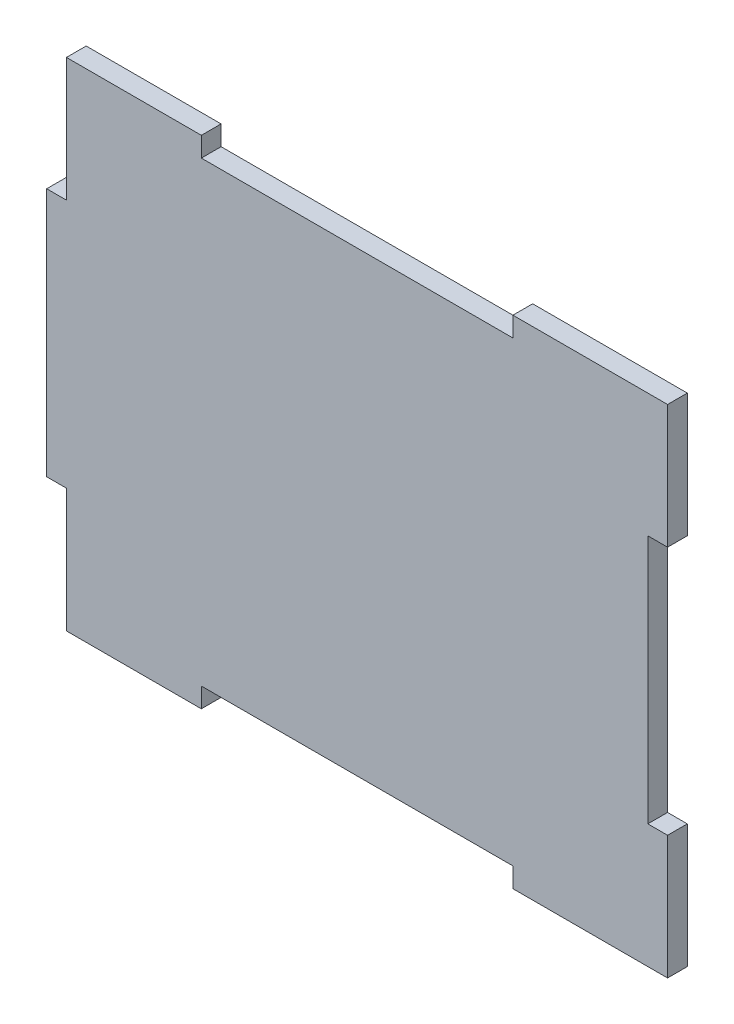
SolidWorks part; units mm, degrees
ref_plane "Front Plane" through (0, 0, 0) normal (0, 0, 1) x (1, 0, 0)
ref_plane "Top Plane" through (0, 0, 0) normal (0, 1, 0) x (1, 0, 0)
ref_plane "Right Plane" through (0, 0, 0) normal (1, 0, 0) x (0, 0, -1)
sketch "Sketch3" plane through (0, 0, 0) normal (0, 0, 1) x (1, 0, 0)
  line L1 (50, -40) -> (-50, -40)
  line L2 (50, -40) -> (50, 40)
  line L3 (50, 40) -> (-50, 40)
  line L4 (-50, -40) -> (-50, 40)
  line L5 (50, -40) -> (-50, 40) construction
  line L6 (50, 40) -> (-50, -40) construction
  point P0 (0, 0)
  dimension "D1" = 100
  dimension "D2" = 80
extrude "Boss-Extrude1" add sketch "Sketch3" along normal blind 3.18
sketch "Sketch4" plane through (0, 0, 3.18) normal (0, 0, 1) x (1, 0, 0)
  line L0 (50, 40) -> (-50, 40) construction
  line L1 (-25.09, 40) -> (25.09, 40)
  line L2 (-25.09, 40) -> (-25.09, 36.82)
  line L3 (-25.09, 36.82) -> (25.09, 36.82)
  line L4 (25.09, 40) -> (25.09, 36.82)
  line L7 (0, 0) -> (0, 96.8251) construction
  point P8 (0, 40)
  dimension "D1" = 3.18
  dimension "D2" = 50.18
extrude "Cut-Extrude1" cut sketch "Sketch4" against normal up to surface (3.18 mm away) up to face at (0, 0, 0)
mirror "Mirror1" about plane through (0, 0, 0) normal (0, 1, 0) of "Cut-Extrude1"
sketch "Sketch5" plane through (0, 0, 3.18) normal (0, 0, 1) x (1, 0, 0)
  line L0 (50, -40) -> (50, 40) construction
  line L1 (50, 20.09) -> (46.82, 20.09)
  line L2 (50, 20.09) -> (50, -20.09)
  line L3 (50, -20.09) -> (46.82, -20.09)
  line L4 (46.82, 20.09) -> (46.82, -20.09)
  line L7 (0, 0) -> (79.7513, 0) construction
  point P8 (50, 0)
  dimension "D1" = 3.18
  dimension "D2" = 40.18
extrude "Cut-Extrude2" cut sketch "Sketch5" against normal up to surface (3.18 mm away) up to face at (0, 0, 0)
sketch "Sketch6" plane through (0, 0, 3.18) normal (0, 0, 1) x (1, 0, 0)
  line L0 (-25.09, 40) -> (-50, 40) construction
  line L1 (-46.82, 40) -> (-50, 40)
  line L2 (-46.82, 40) -> (-46.82, 20.09)
  line L3 (-46.82, 20.09) -> (-50, 20.09)
  line L4 (-50, 40) -> (-50, 20.09)
  line L5 (-50, 40) -> (-50, -40) construction
  line L6 (-50, -40) -> (-25.09, -40) construction
  dimension "D1" = 3.18
  dimension "D3" = 60.09
  dimension "D2" = 19.91
extrude "Cut-Extrude3" cut sketch "Sketch6" against normal up to surface (3.18 mm away) up to face at (12.1025, 0, 0)
mirror "Mirror2" about plane through (0, 0, 0) normal (0, 1, 0) of "Cut-Extrude3"
sketch "Sketch7" [suppressed] plane through (0, 0, 0) normal (0, 0, -1) x (-1, 0, 0)
  line L1 (46.82, -40) -> (46.82, -20.09) construction
  line L2 (-3.18, -25) -> (16.82, -25) construction
  line L4 (-25.09, -40) -> (-50, -40) construction
  circle A0 centre (16.82, -25) radius 3.18
  circle A1 centre (-3.18, -25) radius 3.935
  dimension "D1" = 20
  dimension "D2" = 30
  dimension "D3" = 6.36
  dimension "D4" = 7.87
  dimension "D5" = 15
extrude "Cut-Extrude4" [suppressed] cut sketch "Sketch7" against normal up to surface (3.18 mm away)
sketch "Sketch8" [suppressed] plane through (0, 0, 0) normal (0, 0, -1) x (-1, 0, 0)
  line L1 (-46.82, -20.09) -> (-46.82, 20.09) construction
  line L2 (-25.09, 36.82) -> (25.09, 36.82) construction
  line L3 (-33.52, 23.44) -> (-22.52, 23.44)
  line L4 (-33.52, 23.44) -> (-33.52, 10.94)
  line L5 (-33.52, 10.94) -> (-22.52, 10.94)
  line L6 (-22.52, 23.44) -> (-22.52, 10.94)
  dimension "D1" = 13.38
  dimension "D2" = 13.3
  dimension "D3" = 12.5
  dimension "D4" = 11
extrude "Cut-Extrude5" [suppressed] cut sketch "Sketch8" against normal up to surface (3.18 mm away)
equation "\"h\"= 80"
equation "\"w\"= 100"
equation "\"l\"= 180"
equation "\"kerf\"= 0.18"
equation "\"tablen\"= \"h\" / 2"
equation "\"D1@Sketch3\"=\"w\""
equation "\"D2@Sketch3\"=\"h\""
equation "\"D2@Sketch4\"=50+\"kerf\""
equation "\"D2@Sketch5\"=40+\"kerf\""
equation "\"D2@Sketch6\"=20-\"kerf\"/2"
